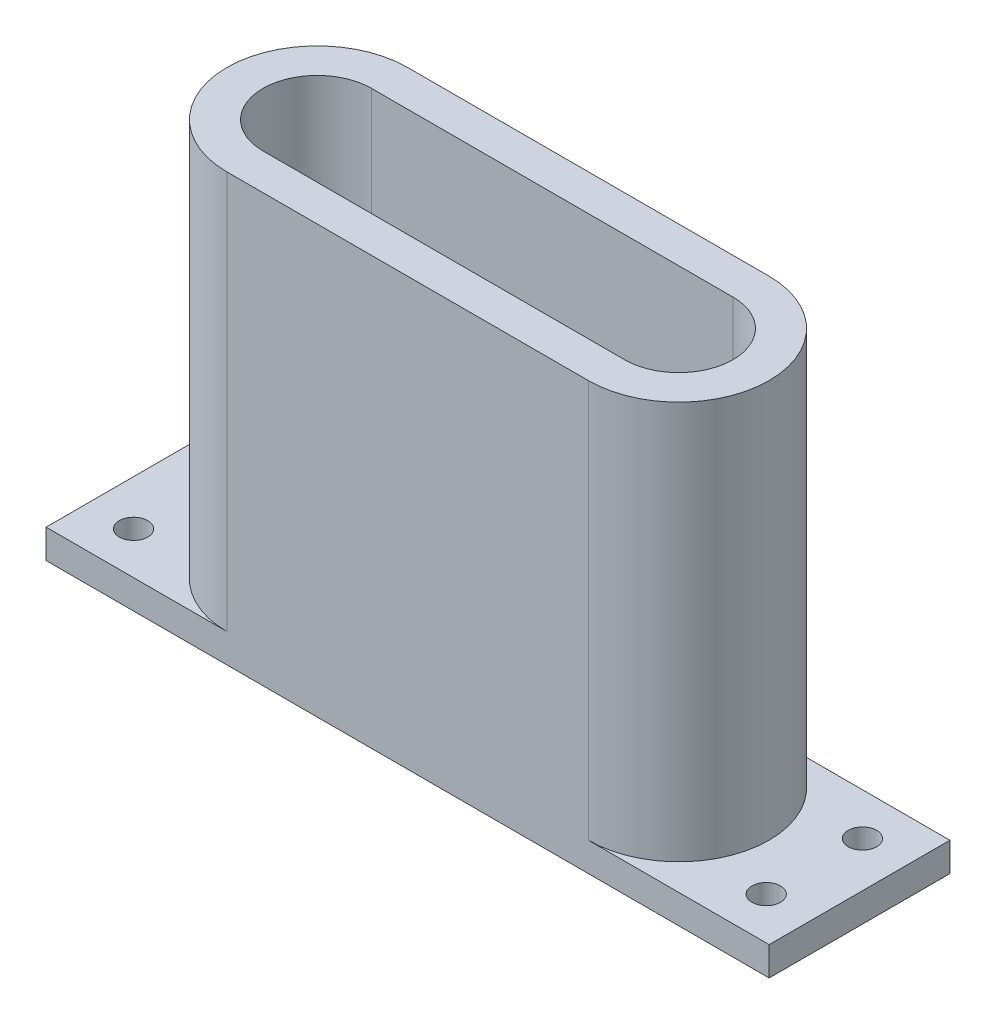
SolidWorks part; units mm, degrees
ref_plane "Front Plane" through (0, 0, 0) normal (0, 0, 1) x (1, 0, 0)
ref_plane "Top Plane" through (0, 0, 0) normal (0, 1, 0) x (1, 0, 0)
ref_plane "Right Plane" through (0, 0, 0) normal (1, 0, 0) x (0, 0, -1)
sketch "Sketch1" plane through (0, 0, 0) normal (0, 1, 0) x (1, 0, 0)
  line L1 (-25.4, -12.7) -> (25.4, -12.7)
  line L2 (-25.4, 12.7) -> (25.4, 12.7)
  line L4 (-25.4, -12.7) -> (25.4, 12.7) construction
  line L5 (-25.4, 12.7) -> (25.4, -12.7) construction
  line L6 (-38.1, 0) -> (38.1, 0) construction
  line L7 (-25.4, -7.62) -> (25.4, -7.62)
  line L8 (-25.4, 7.62) -> (25.4, 7.62)
  arc A0 (-25.4, 12.7) -> (-25.4, -12.7) centre (-25.4, 0) ccw
  arc A2 (25.4, -12.7) -> (25.4, 12.7) centre (25.4, 0) ccw
  arc A3 (-25.4, 7.62) -> (-25.4, -7.62) centre (-25.4, 0) ccw
  arc A4 (25.4, -7.62) -> (25.4, 7.62) centre (25.4, 0) ccw
  point P1 (0, 0)
  point P17 (0, 0)
  point P19 (38.1, 0)
  dimension "D1" = 76.2
  dimension "D2" = 25.4
  dimension "D3" = 5.08
extrude "Boss-Extrude1" add sketch "Sketch1" along normal blind 60
sketch "Sketch2" plane through (0, 0, 0) normal (0, -1, 0) x (1, 0, 0)
  line L0 (-50.8, -12.7) -> (50.8, -12.7)
  line L1 (-50.8, -12.7) -> (-50.8, 12.7)
  line L2 (50.8, -12.7) -> (50.8, 12.7)
  line L3 (-50.8, 12.7) -> (50.8, 12.7)
  line L4 (-50.8, -12.7) -> (50.8, 12.7) construction
  line L5 (50.8, -12.7) -> (-50.8, 12.7) construction
  line L6 (-25.4, 12.7) -> (25.4, 12.7) construction
  line L13 (-38.1, 0) -> (-50.8, 0) construction
  line L14 (-44.45, 6.7629) -> (-44.45, -6.7629) construction
  line L15 (-25.4, -7.62) -> (25.4, -7.62)
  line L16 (25.4, 7.62) -> (-25.4, 7.62)
  line L17 (-25.4, -7.62) -> (25.4, -7.62)
  line L18 (25.4, 7.62) -> (-25.4, 7.62)
  line L19 (0, 0) -> (0, 32.7118) construction
  arc A0 (25.4, -12.7) -> (25.4, 12.7) centre (25.4, 0) ccw construction
  arc A6 (-25.4, 12.7) -> (-25.4, -12.7) centre (-25.4, 0) ccw construction
  arc A7 (25.4, -7.62) -> (25.4, 7.62) centre (25.4, 0) ccw
  arc A8 (-25.4, 7.62) -> (-25.4, -7.62) centre (-25.4, 0) ccw
  arc A9 (25.4, -7.62) -> (25.4, 7.62) centre (25.4, 0) ccw
  arc A10 (-25.4, 7.62) -> (-25.4, -7.62) centre (-25.4, 0) ccw
  circle A11 centre (-44.45, -6.7629) radius 2
  circle A12 centre (-44.45, 6.7629) radius 2
  circle A13 centre (44.45, 6.7629) radius 2
  circle A14 centre (44.45, -6.7629) radius 2
  point P1 (0, 0)
  point P18 (-44.45, 0)
  point P19 (-44.45, 0)
  dimension "D1" = 25.4
  dimension "D3" = 4
  dimension "D2" = 0
extrude "Boss-Extrude2" add sketch "Sketch2" against normal blind 4.064
